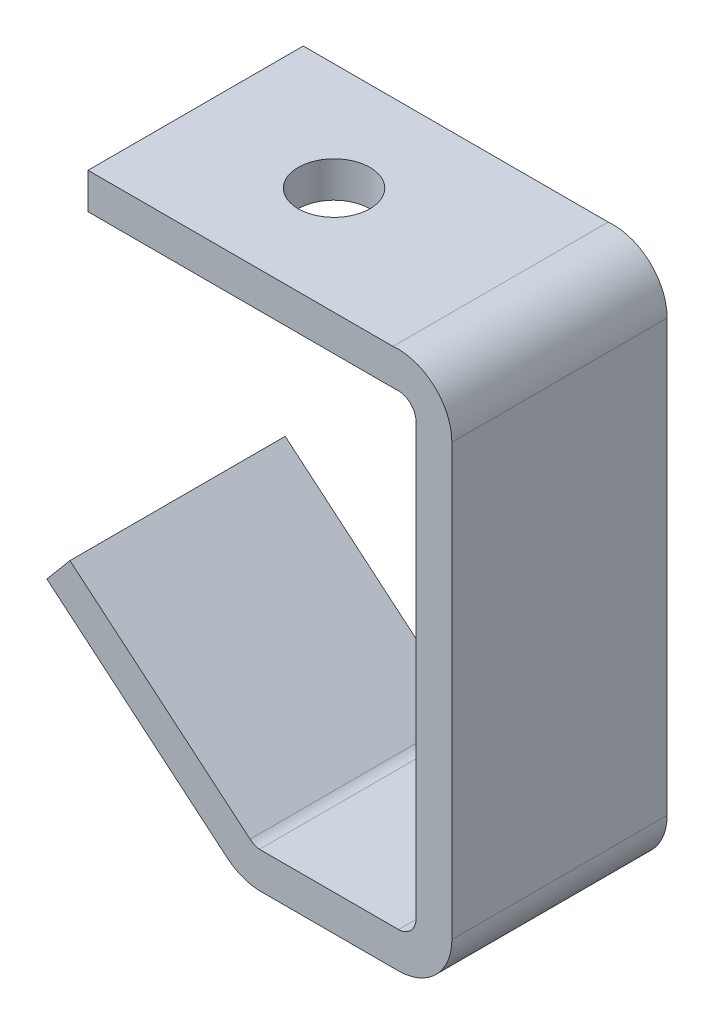
SolidWorks part; units mm, degrees
ref_plane "Front Plane" through (0, 0, 0) normal (0, 0, 1) x (1, 0, 0)
ref_plane "Top Plane" through (0, 0, 0) normal (0, 1, 0) x (1, 0, 0)
ref_plane "Right Plane" through (0, 0, 0) normal (1, 0, 0) x (0, 0, -1)
sketch "Sketch1" plane through (0, 0, 0) normal (0, 0, 1) x (1, 0, 0)
  line L0 (0, 0) -> (53.98, 0)
  line L1 (64.4014, -9.4882) -> (64.4014, -85.7212)
  line L2 (55.0251, -95.25) -> (30.0713, -95.25)
  line L3 (24.6021, -93.043) -> (-7.2807, -66.2902)
  line L4 (0, -6.35) -> (54.3576, -6.35)
  line L5 (58.0514, -9.4882) -> (58.0514, -85.7212)
  line L6 (54.9602, -88.9) -> (30.3491, -88.9)
  line L7 (28.6838, -88.1787) -> (-3.199, -61.4258)
  line L8 (0, 0) -> (0, -6.35)
  line L9 (-3.199, -61.4258) -> (-7.2807, -66.2902)
  arc A0 (53.98, 0) -> (64.4014, -9.4882) centre (54.8714, -9.4882) cw
  arc A1 (64.4014, -85.7212) -> (55.0251, -95.25) centre (54.8714, -85.7212) cw
  arc A2 (30.0713, -95.25) -> (24.6021, -93.043) centre (30.7279, -85.7426) cw
  arc A3 (54.3576, -6.35) -> (58.0514, -9.4882) centre (54.8714, -9.4882) cw
  arc A4 (58.0514, -85.7212) -> (54.9602, -88.9) centre (54.8714, -85.7212) cw
  arc A5 (30.3491, -88.9) -> (28.6838, -88.1787) centre (30.7279, -85.7426) cw
  dimension "D2" = 9.53
  dimension "D3" = 9.53
  dimension "D4" = 9.53
  dimension "D1" = 53.98
  dimension "D5" = 95.25
  dimension "D6" = 24.9538
  dimension "D7" = 41.62
  dimension "D8" = 140
  dimension "D9" = 6.35
extrude "Boss-Extrude1" add sketch "Sketch1" along normal blind 38.1
sketch "Sketch2" plane through (0, 0, 0) normal (0, 1, 0) x (1, 0, 0)
  line L0 (0, -19.05) -> (24.5, -19.05)
  line L1 (0, -38.1) -> (0, 0) construction
  circle A0 centre (24.5, -19.05) radius 6.35
  dimension "D2" = 12.7
  dimension "D1" = 24.5
extrude "Cut-Extrude1" cut sketch "Sketch2" against normal blind 38.1
